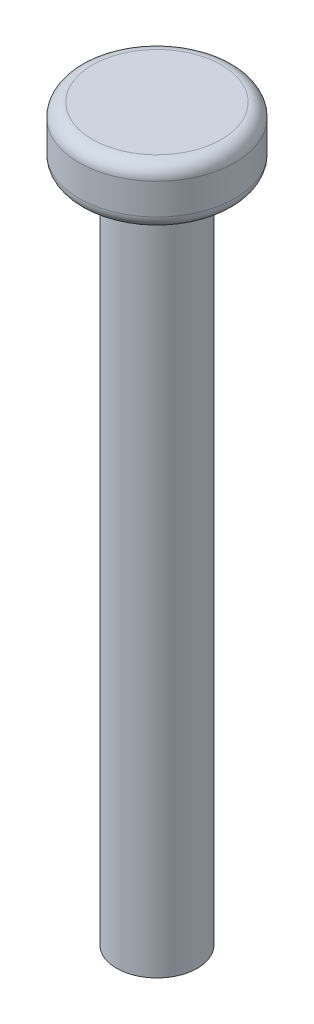
SolidWorks part; units mm, degrees
ref_plane "Спереди" through (0, 0, 0) normal (0, 0, 1) x (1, 0, 0)
ref_plane "Сверху" through (0, 0, 0) normal (0, 1, 0) x (1, 0, 0)
ref_plane "Справа" through (0, 0, 0) normal (1, 0, 0) x (0, 0, -1)
sketch "Sketch1" plane through (0, 0, 0) normal (0, 1, 0) x (1, 0, 0)
  circle A0 centre (0, 0) radius 3
  dimension "D1" = 6
extrude "Boss-Extrude1" add sketch "Sketch1" along normal blind 50
sketch "Sketch2" plane through (0, 50, 0) normal (0, 1, 0) x (1, 0, 0)
  circle A0 centre (0, 0) radius 5.8
  dimension "D1" = 11.6
extrude "Boss-Extrude2" add sketch "Sketch2" along normal blind 4.3
fillet "Fillet1" radius 1 2 edges at (0, 50, 5.8) (0, 54.3, 5.8)
